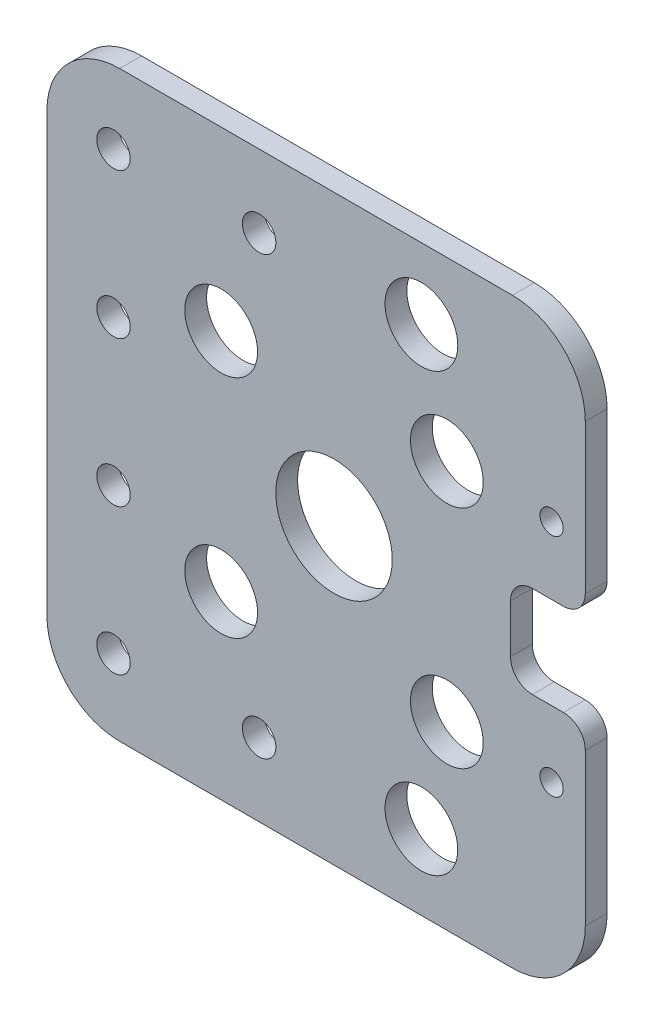
SolidWorks part; units mm, degrees
ref_plane "Front Plane" through (0, 0, 0) normal (0, 0, 1) x (1, 0, 0)
ref_plane "Top Plane" through (0, 0, 0) normal (0, 1, 0) x (1, 0, 0)
ref_plane "Right Plane" through (0, 0, 0) normal (1, 0, 0) x (0, 0, -1)
sketch "Sketch1" plane through (0, 0, 0) normal (0, 0, 1) x (1, 0, 0)
  line L0 (157.9607, -71.8662) -> (170.4739, -71.8662)
  line L1 (116.5258, -71.8662) -> (157.9607, -71.8662)
  line L2 (106.5258, -81.8662) -> (106.5258, -141.8968)
  line L3 (116.5258, -151.8968) -> (157.9607, -151.8968)
  line L4 (180.4739, -81.8662) -> (180.4739, -102.3655)
  line L5 (145.9607, -111.5917) -> (157.9607, -111.5917) construction
  line L6 (157.9607, -111.5917) -> (157.9607, -81.5917) construction
  line L7 (157.9607, -111.5917) -> (157.9607, -141.5917) construction
  line L8 (170.4739, -151.8968) -> (157.9607, -151.8968)
  line L9 (180.4739, -120.9895) -> (180.4739, -141.8968)
  line L10 (180.4739, -102.3655) -> (180.4739, -105.3655)
  line L11 (180.4739, -105.3655) -> (170.1989, -105.3655)
  line L12 (170.1989, -133.8871) -> (170.1989, -89.8565) construction
  line L13 (180.4739, -120.9895) -> (180.4739, -117.9895)
  line L14 (180.4739, -117.9895) -> (170.1989, -117.9895)
  line L15 (170.1989, -105.3655) -> (170.1989, -117.9895)
  circle A0 centre (115.6746, -101.8662) radius 2.3
  circle A1 centre (115.6746, -121.8662) radius 2.3
  circle A2 centre (135.6746, -141.8662) radius 2.3
  circle A3 centre (135.6746, -81.8662) radius 2.3
  circle A4 centre (115.6746, -81.8662) radius 2.3
  circle A5 centre (115.6746, -141.8662) radius 2.3
  circle A6 centre (161.4607, -96.1142) radius 5
  circle A7 centre (161.4607, -127.1142) radius 5
  circle A8 centre (130.4607, -96.1142) radius 5
  arc A9 (180.4739, -141.8968) -> (170.4739, -151.8968) centre (170.4739, -141.8968) cw
  circle A10 centre (145.9607, -111.5917) radius 8
  arc A11 (180.4739, -81.8662) -> (170.4739, -71.8662) centre (170.4739, -81.8662) ccw
  circle A12 centre (175.8433, -96.1142) radius 1.6
  arc A13 (106.5258, -141.8968) -> (116.5258, -151.8968) centre (116.5258, -141.8968) ccw
  arc A14 (116.5258, -71.8662) -> (106.5258, -81.8662) centre (116.5258, -81.8662) ccw
  circle A15 centre (157.9607, -81.5917) radius 5
  circle A16 centre (157.9607, -141.5917) radius 5
  circle A17 centre (175.8433, -127.1142) radius 1.6
  circle A18 centre (130.4607, -127.1142) radius 5
  point P47 (106.5258, -71.8662)
  dimension "D1" = 10
  dimension "D4" = 12
  dimension "D5" = 3
  dimension "D2" = 30
  dimension "D3" = 30
  dimension "D6" = 3
extrude "Boss-Extrude1" add sketch "Sketch1" along normal blind 3
fillet "Fillet1" radius 3 4 edges at (170.1989, -117.9895, 1.5) (180.4739, -117.9895, 1.5) (170.1989, -105.3655, 1.5) (180.4739, -105.3655, 1.5)
